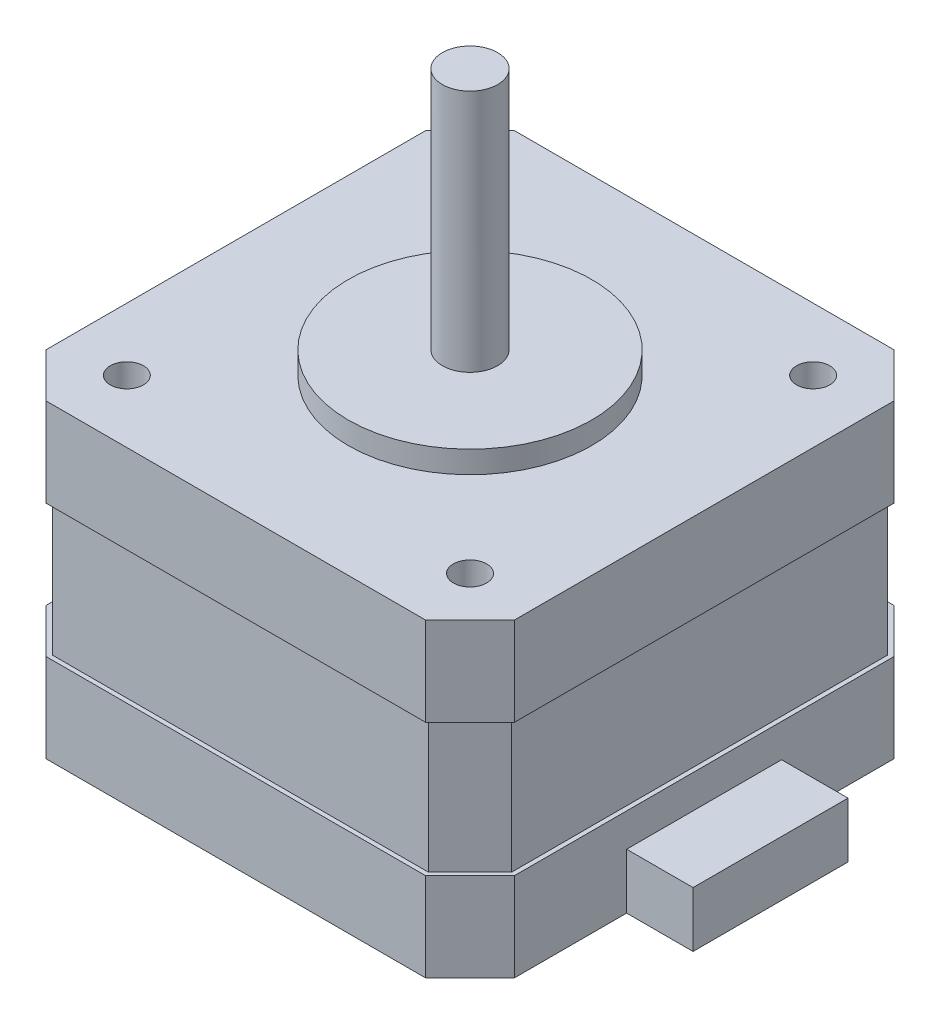
SolidWorks part; units mm, degrees
material "Простая углеродистая сталь"
ref_plane "Спереди" through (0, 0, 0) normal (0, 0, 1) x (1, 0, 0)
ref_plane "Сверху" through (0, 0, 0) normal (0, 1, 0) x (1, 0, 0)
ref_plane "Справа" through (0, 0, 0) normal (1, 0, 0) x (0, 0, -1)
other "Configuration Table"
sketch "Эскиз2" plane through (0, 0, 0) normal (0, 1, 0) x (1, 0, 0)
  line L1 (-21.15, -21.15) -> (21.15, -21.15)
  line L2 (-21.15, -21.15) -> (-21.15, 21.15)
  line L3 (-21.15, 21.15) -> (21.15, 21.15)
  line L4 (21.15, -21.15) -> (21.15, 21.15)
  line L5 (-21.15, -21.15) -> (21.15, 21.15) construction
  line L6 (-21.15, 21.15) -> (21.15, -21.15) construction
  point P0 (0, 0)
  dimension "D1" = 42.3
extrude "Бобышка-Вытянуть1" add sketch "Эскиз2" along normal blind 28
sketch "Эскиз3" plane through (0, 28, 0) normal (0, 1, 0) x (1, 0, 0)
  circle A0 centre (0, 0) radius 11
  dimension "D1" = 22
extrude "Бобышка-Вытянуть2" add sketch "Эскиз3" along normal blind 2
sketch "Эскиз4" plane through (0, 30, 0) normal (0, 1, 0) x (1, 0, 0)
  circle A0 centre (0, 0) radius 2.5
  dimension "D1" = 5
extrude "Бобышка-Вытянуть3" add sketch "Эскиз4" along normal blind 24 from surface at -2 starting at face at (0, 28, 11)
sketch "Эскиз5" plane through (0, 28, 0) normal (0, 1, 0) x (1, 0, 0)
  line L1 (-15.5, 15.5) -> (15.5, 15.5) construction
  line L2 (-15.5, 15.5) -> (-15.5, -15.5) construction
  line L3 (-15.5, -15.5) -> (15.5, -15.5) construction
  line L4 (15.5, 15.5) -> (15.5, -15.5) construction
  circle A4 centre (-15.5, 15.5) radius 1.5
  circle A5 centre (15.5, 15.5) radius 1.5
  circle A6 centre (15.5, -15.5) radius 1.5
  circle A7 centre (-15.5, -15.5) radius 1.5
  point P4 (0, 15.5)
  point P5 (-15.5, 0)
  dimension "D2" = 3
  dimension "D1" = 31
extrude "Вырез-Вытянуть1" cut sketch "Эскиз5" against normal blind 4.5
chamfer "Фаска1" distance 4 angle 45 4 edges at (-21.15, 14, 21.15) (21.15, 14, 21.15) (-21.15, 14, -21.15) (21.15, 14, -21.15)
sketch "Эскиз6" plane through (0, 28, 0) normal (0, 1, 0) x (1, 0, 0)
  line L16 (-20.75, 16.9843) -> (-20.75, -16.9843)
  line L17 (-20.75, -16.9843) -> (-16.9843, -20.75)
  line L18 (-16.9843, -20.75) -> (16.9843, -20.75)
  line L19 (16.9843, -20.75) -> (20.75, -16.9843)
  line L20 (20.75, -16.9843) -> (20.75, 16.9843)
  line L21 (20.75, 16.9843) -> (16.9843, 20.75)
  line L22 (16.9843, 20.75) -> (-16.9843, 20.75)
  line L23 (-16.9843, 20.75) -> (-20.75, 16.9843)
  line L24 (-20.75, 16.9843) -> (-20.75, -16.9843)
  line L25 (-20.75, -16.9843) -> (-16.9843, -20.75)
  line L26 (-16.9843, -20.75) -> (16.9843, -20.75)
  line L27 (16.9843, -20.75) -> (20.75, -16.9843)
  line L28 (20.75, -16.9843) -> (20.75, 16.9843)
  line L29 (20.75, 16.9843) -> (16.9843, 20.75)
  line L30 (16.9843, 20.75) -> (-16.9843, 20.75)
  line L31 (-16.9843, 20.75) -> (-20.75, 16.9843)
  dimension "D1" = 0.4
extrude "Вырез-Вытянуть2" cut sketch "Эскиз6" against normal offset from surface (12 mm away) 8 from offset 8 flip side to cut up to face at (0, 0, 0) offset against normal yes
sketch "Эскиз7" plane through (0, 0, 0) normal (0, -1, 0) x (1, 0, 0)
  circle A0 centre (-15.5, -15.5) radius 2.5
  circle A1 centre (15.5, -15.5) radius 2.5
  circle A2 centre (15.5, 15.5) radius 2.5
  circle A3 centre (-15.5, 15.5) radius 2.5
  dimension "D1" = 5
extrude "Бобышка-Вытянуть4" add sketch "Эскиз7" along normal blind 2
chamfer "Фаска2" distance 1 angle 45 4 edges at (-15.5, -2, 13) (15.5, -2, 13) (-15.5, -2, -18) (15.5, -2, -18)
sketch "Эскиз8" plane through (21.15, 0, 0) normal (1, 0, 0) x (0, 0, -1)
  line L0 (-17.15, 0) -> (17.15, 0) construction
  line L1 (-7, 0) -> (7, 0)
  line L2 (-7, 0) -> (-7, 5)
  line L3 (-7, 5) -> (7, 5)
  line L4 (7, 0) -> (7, 5)
  point P7 (0, 0)
  point P8 (0, 0)
  dimension "D1" = 14
  dimension "D2" = 5
extrude "Бобышка-Вытянуть5" add sketch "Эскиз8" along normal blind 6
